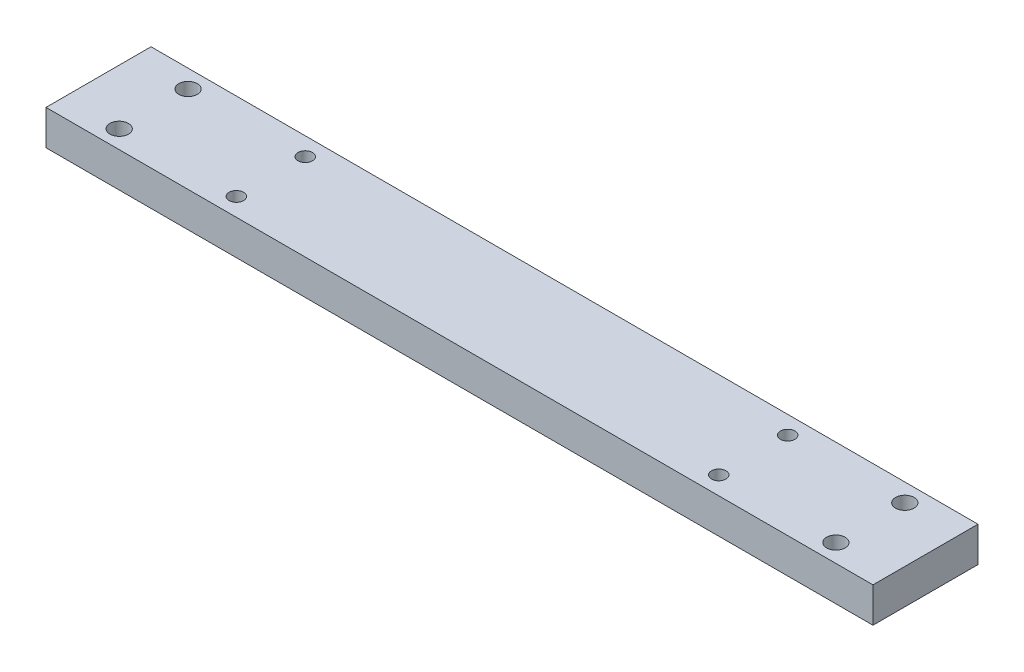
SolidWorks part; units mm, degrees
ref_plane "Front Plane" through (0, 0, 0) normal (0, 0, 1) x (1, 0, 0)
ref_plane "Top Plane" through (0, 0, 0) normal (0, 1, 0) x (1, 0, 0)
ref_plane "Right Plane" through (0, 0, 0) normal (1, 0, 0) x (0, 0, -1)
sketch "Sketch1" plane through (0, 0, 0) normal (0, 1, 0) x (1, 0, 0)
  line L1 (0, 0) -> (600, 0)
  line L2 (0, 0) -> (0, 76.2)
  line L3 (0, 76.2) -> (600, 76.2)
  line L4 (600, 0) -> (600, 76.2)
  dimension "D1" = 600
  dimension "D2" = 76.2
extrude "Boss-Extrude1" add sketch "Sketch1" along normal blind 25.4
sketch "Sketch2" plane through (0, 25.4, 0) normal (0, 1, 0) x (1, 0, 0)
  line L1 (0, 0) -> (300, 0)
  line L2 (0, 0) -> (0, 38.1)
  line L3 (0, 38.1) -> (300, 38.1)
  line L4 (300, 0) -> (300, 38.1)
  line L5 (40, 63.1) -> (560, 63.1)
  line L6 (40, 63.1) -> (40, 13.1)
  line L7 (40, 13.1) -> (560, 13.1)
  line L8 (560, 63.1) -> (560, 13.1)
  line L9 (40, 63.1) -> (560, 13.1) construction
  line L10 (40, 13.1) -> (560, 63.1) construction
  circle A0 centre (40, 63.1) radius 6.75
  circle A1 centre (40, 13.1) radius 6.75
  circle A2 centre (560, 13.1) radius 6.75
  circle A3 centre (560, 63.1) radius 6.75
  dimension "D1" = 300
  dimension "D2" = 38.1
  dimension "D3" = 520
  dimension "D4" = 50
extrude "Cut-Extrude1" cut sketch "Sketch2" against normal blind 25.4 contours A2 | A3 | A1 | A0
sketch "Sketch3" plane through (0, 25.4, 0) normal (0, 1, 0) x (1, 0, 0)
  line L1 (0, 0) -> (300, 0)
  line L2 (0, 0) -> (0, 38.1)
  line L3 (0, 38.1) -> (300, 38.1)
  line L4 (300, 0) -> (300, 38.1)
  line L5 (125, 63.1) -> (475, 63.1)
  line L6 (125, 63.1) -> (125, 13.1)
  line L7 (125, 13.1) -> (475, 13.1)
  line L8 (475, 63.1) -> (475, 13.1)
  line L9 (125, 63.1) -> (475, 13.1) construction
  line L10 (125, 13.1) -> (475, 63.1) construction
  circle A0 centre (125, 63.1) radius 5.25
  circle A1 centre (125, 13.1) radius 5.25
  circle A2 centre (475, 13.1) radius 5.25
  circle A3 centre (475, 63.1) radius 5.25
  dimension "D1" = 300
  dimension "D2" = 38.1
  dimension "D3" = 350
  dimension "D4" = 50
extrude "Cut-Extrude2" cut sketch "Sketch3" against normal blind 25.4 contours A0 | A1 | A2 | A3
